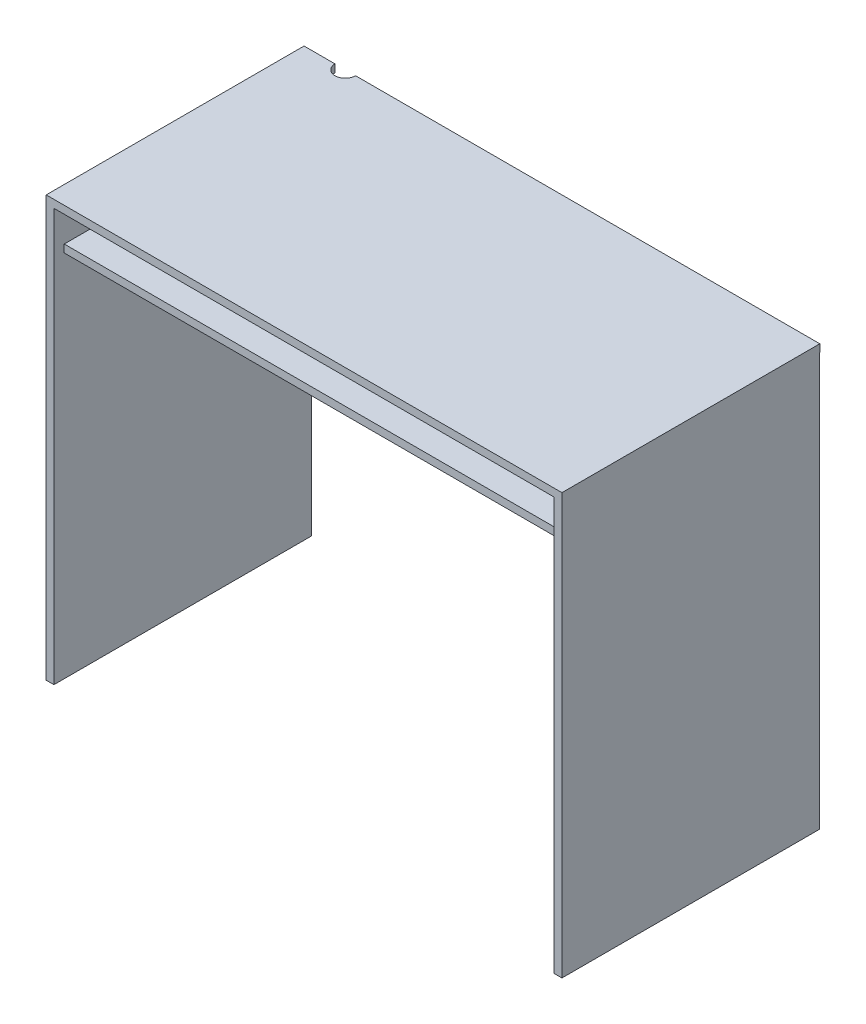
SolidWorks part; units mm, degrees
ref_plane "Front Plane" through (0, 0, 0) normal (0, 0, 1) x (1, 0, 0)
ref_plane "Top Plane" through (0, 0, 0) normal (0, 1, 0) x (1, 0, 0)
ref_plane "Right Plane" through (0, 0, 0) normal (1, 0, 0) x (0, 0, -1)
sketch "Sketch1" plane through (0, 0, 0) normal (0, 1, 0) x (1, 0, 0)
  line L1 (-500, -250) -> (500, -250)
  line L2 (-500, -250) -> (-500, 250)
  line L3 (-500, 250) -> (500, 250)
  line L4 (500, -250) -> (500, 250)
  line L5 (-500, -250) -> (500, 250) construction
  line L6 (-500, 250) -> (500, -250) construction
  point P0 (0, 0)
  dimension "D1" = 1000
  dimension "D2" = 500
extrude "Boss-Extrude1" add sketch "Sketch1" along normal blind 15
sketch "Sketch2" plane through (0, 0, 0) normal (0, -1, 0) x (1, 0, 0)
  line L0 (-500, 250) -> (-485, 250)
  line L1 (-500, 250) -> (-500, -249.5096)
  line L2 (-485, 250) -> (-485, -249.5096)
  line L3 (-500, -249.5096) -> (-485, -249.5096)
  line L4 (-500, 250) -> (500, 250) construction
  line L6 (0, 0) -> (0, 23.8661) construction
  line L7 (0, 0) -> (0, 402.585) construction
  line L8 (500, -249.5096) -> (485, -249.5096)
  line L9 (500, 250) -> (485, 250)
  line L10 (500, 250) -> (500, -249.5096)
  line L11 (485, 250) -> (485, -249.5096)
  dimension "D1" = 15
extrude "Boss-Extrude2" add sketch "Sketch2" along normal blind 800
sketch "Sketch3" plane through (-485, 0, 0) normal (1, 0, 0) x (0, 0, -1)
  line L0 (-250, 0) -> (-250, -70) construction
  line L1 (-250, -800) -> (-250, 0) construction
  line L2 (-250, -70) -> (-230, -70) construction
  line L3 (-230, -70) -> (-230, -85)
  line L4 (-230, -70) -> (229.5096, -70)
  line L5 (-230, -85) -> (229.5096, -85)
  line L6 (229.5096, -70) -> (229.5096, -85)
  line L7 (249.5096, -70) -> (229.5096, -70) construction
  line L8 (249.5096, -800) -> (249.5096, 0) construction
  point P13 (0, 0)
  point P14 (0, 0)
  dimension "D1" = 70
  dimension "D2" = 20
  dimension "D3" = 15
  dimension "D4" = 20
extrude "Boss-Extrude3" add sketch "Sketch3" along normal up to next
sketch "Sketch4" plane through (0, 15, 0) normal (0, 1, 0) x (1, 0, 0)
  line L0 (500, 250) -> (-500, 250) construction
  circle A0 centre (-420, 250) radius 20
  dimension "D1" = 40
  dimension "D2" = 80
extrude "Cut-Extrude1" cut sketch "Sketch4" against normal through all
